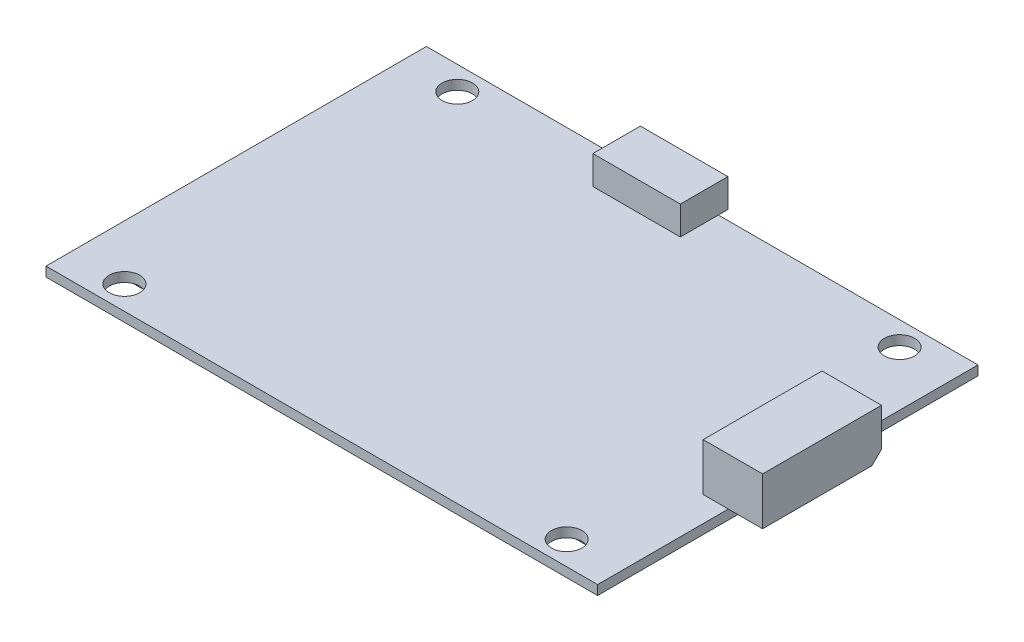
SolidWorks part; units mm, degrees
ref_plane "Front Plane" through (0, 0, 0) normal (0, 0, 1) x (1, 0, 0)
ref_plane "Top Plane" through (0, 0, 0) normal (0, 1, 0) x (1, 0, 0)
ref_plane "Right Plane" through (0, 0, 0) normal (1, 0, 0) x (0, 0, -1)
sketch "Sketch1" plane through (0, 0, 0) normal (0, 1, 0) x (1, 0, 0)
  line L1 (29, -20) -> (-29, -20)
  line L2 (29, -20) -> (29, 20)
  line L3 (29, 20) -> (-29, 20)
  line L4 (-29, -20) -> (-29, 20)
  line L5 (29, -20) -> (-29, 20) construction
  line L6 (29, 20) -> (-29, -20) construction
  point P0 (0, 0)
  dimension "D1" = 40
  dimension "D2" = 58
extrude "Boss-Extrude1" add sketch "Sketch1" along normal blind 1
sketch "Sketch2" plane through (0, 1, 0) normal (0, 1, 0) x (1, 0, 0)
  line L0 (29, -20) -> (29, 20) construction
  line L1 (26.35, 6.25) -> (32.6, 6.25)
  line L2 (26.35, 6.25) -> (26.35, -6.25)
  line L3 (26.35, -6.25) -> (32.6, -6.25)
  line L4 (32.6, 6.25) -> (32.6, -6.25)
  line L5 (-29, -20) -> (29, -20) construction
  dimension "D1" = 12.5
  dimension "D2" = 6.25
  dimension "D3" = 3.6
  dimension "D4" = 13.75
extrude "Boss-Extrude2" add sketch "Sketch2" along normal blind 5
chamfer "Chamfer1" distance 1 angle 45 1 edges at (30.8, 1, -6.25)
sketch "Sketch3" plane through (0, 1, 0) normal (0, 1, 0) x (1, 0, 0)
  line L0 (29, 20) -> (-29, 20) construction
  line L1 (-7.5, 21) -> (1.7, 21)
  line L2 (-7.5, 21) -> (-7.5, 16)
  line L3 (-7.5, 16) -> (1.7, 16)
  line L4 (1.7, 21) -> (1.7, 16)
  line L5 (-29, 20) -> (-29, -20) construction
  dimension "D1" = 9.2
  dimension "D2" = 5
  dimension "D3" = 1
  dimension "D4" = 21.5
extrude "Boss-Extrude3" add sketch "Sketch3" along normal blind 3
sketch "Sketch4" plane through (0, 0, 0) normal (0, -1, 0) x (1, 0, 0)
  line L0 (-29, 20) -> (29, 20) construction
  line L1 (-28, 12) -> (-23, 12)
  line L2 (-28, 12) -> (-28, 5.4)
  line L3 (-28, 5.4) -> (-23, 5.4)
  line L4 (-23, 12) -> (-23, 5.4)
  line L5 (-28, -5.6) -> (-23, -5.6)
  line L6 (-28, -5.6) -> (-28, -12.2)
  line L7 (-28, -12.2) -> (-23, -12.2)
  line L8 (-23, -5.6) -> (-23, -12.2)
  line L9 (17.5, 12) -> (22.5, 12)
  line L10 (17.5, 12) -> (17.5, 5.4)
  line L11 (17.5, 5.4) -> (22.5, 5.4)
  line L12 (22.5, 12) -> (22.5, 5.4)
  line L13 (17.5, -5.6) -> (22.5, -5.6)
  line L14 (17.5, -5.6) -> (17.5, -12.2)
  line L15 (17.5, -12.2) -> (22.5, -12.2)
  line L16 (22.5, -5.6) -> (22.5, -12.2)
  line L17 (-29, -20) -> (-29, 20) construction
  line L18 (29, 20) -> (29, -20) construction
  dimension "D1" = 6.6
  dimension "D2" = 5
  dimension "D3" = 8
  dimension "D4" = 1
  dimension "D5" = 11
  dimension "D6" = 6.5
extrude "Boss-Extrude4" add sketch "Sketch4" along normal blind 4
sketch "Sketch5" plane through (0, 1, 0) normal (0, 1, 0) x (1, 0, 0)
  line L0 (0, 0) -> (0, -50000) construction
  line L1 (0, 0) -> (-50000, 0) construction
  circle A0 centre (-23.25, 17.5) radius 1.6
  circle A1 centre (-23.25, -17.5) radius 1.6
  circle A2 centre (23.25, -17.5) radius 1.6
  circle A3 centre (23.25, 17.5) radius 1.6
  point P13 (0, 0)
  point P14 (0, 0)
  point P15 (0, 0)
  point P16 (0, 0)
  dimension "D1" = 3.2
  dimension "D2" = 35
  dimension "D3" = 46.5
extrude "Cut-Extrude1" cut sketch "Sketch5" against normal through all
